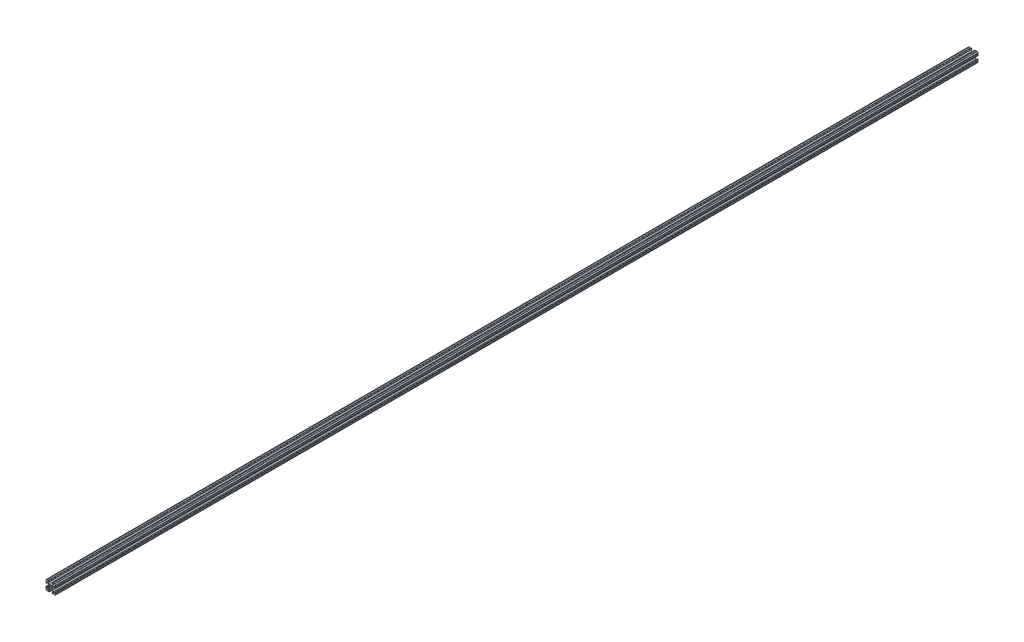
SolidWorks part; units mm, degrees
ref_plane "Front Plane" through (0, 0, 0) normal (0, 0, 1) x (1, 0, 0)
ref_plane "Top Plane" through (0, 0, 0) normal (0, 1, 0) x (1, 0, 0)
ref_plane "Right Plane" through (0, 0, 0) normal (1, 0, 0) x (0, 0, -1)
sketch "Sketch1" plane through (0, 0, 0) normal (0, 0, 1) x (1, 0, 0)
  line L0 (-12.7, -6.3331) -> (-12.7, -9.5504)
  line L1 (-9.5504, -12.7) -> (-6.3331, -12.7)
  line L2 (-5.3171, -12.7) -> (-4.3434, -12.7)
  line L3 (-4.3434, -10.4902) -> (-6.4748, -10.4902)
  line L4 (-7.1932, -8.7558) -> (-3.8632, -5.4257)
  line L5 (-1.6181, -4.4958) -> (1.6181, -4.4958)
  line L6 (3.8632, -5.4257) -> (7.1932, -8.7558)
  line L7 (6.4748, -10.4902) -> (4.3434, -10.4902)
  line L8 (4.3434, -12.7) -> (5.3171, -12.7)
  line L9 (6.3331, -12.7) -> (9.5504, -12.7)
  line L10 (12.7, -9.5504) -> (12.7, -6.3331)
  line L11 (12.7, -5.3171) -> (12.7, -4.3434)
  line L12 (10.4902, -4.3434) -> (10.4902, -6.4748)
  line L13 (8.7558, -7.1932) -> (5.4257, -3.8632)
  line L14 (4.4958, -1.6181) -> (4.4958, 1.6181)
  line L15 (5.4257, 3.8632) -> (8.7558, 7.1932)
  line L16 (10.4902, 6.4748) -> (10.4902, 4.3434)
  line L17 (12.7, 4.3434) -> (12.7, 5.3171)
  line L18 (12.7, 6.3331) -> (12.7, 9.5504)
  line L19 (9.5504, 12.7) -> (6.3331, 12.7)
  line L20 (5.3171, 12.7) -> (4.3434, 12.7)
  line L21 (4.3434, 10.4902) -> (6.4748, 10.4902)
  line L22 (7.1932, 8.7558) -> (3.8632, 5.4257)
  line L23 (1.6181, 4.4958) -> (-1.6181, 4.4958)
  line L24 (-3.8632, 5.4257) -> (-7.1932, 8.7558)
  line L25 (-6.4748, 10.4902) -> (-4.3434, 10.4902)
  line L26 (-4.3434, 12.7) -> (-5.3171, 12.7)
  line L27 (-6.3331, 12.7) -> (-9.5504, 12.7)
  line L28 (-12.7, 9.5504) -> (-12.7, 6.3331)
  line L29 (-12.7, 5.3171) -> (-12.7, 4.3434)
  line L30 (-10.4902, 4.3434) -> (-10.4902, 6.4748)
  line L31 (-8.7558, 7.1932) -> (-5.4257, 3.8632)
  line L32 (-4.4958, 1.6181) -> (-4.4958, -1.6181)
  line L33 (-5.4257, -3.8632) -> (-8.7558, -7.1932)
  line L34 (-10.4902, -6.4748) -> (-10.4902, -4.3434)
  line L35 (-12.7, -4.3434) -> (-12.7, -5.3171)
  circle A0 centre (0, 0) radius 2.6035
  arc A1 (-12.7, -5.3171) -> (-12.7, -6.3331) centre (-12.7, -5.8251) cw
  arc A2 (-12.7, -9.5504) -> (-12.6998, -10.5664) centre (-12.7, -10.0584) cw
  arc A3 (-12.6998, -10.5664) -> (-10.5664, -12.6998) centre (-10.5918, -10.5918) ccw
  arc A4 (-10.5664, -12.6998) -> (-9.5504, -12.7) centre (-10.0584, -12.7) cw
  arc A5 (-6.3331, -12.7) -> (-5.3171, -12.7) centre (-5.8251, -12.7) cw
  arc A6 (-4.3434, -12.7) -> (-4.3434, -10.4902) centre (-4.3434, -11.5951) ccw
  arc A7 (-6.4748, -10.4902) -> (-7.1932, -8.7558) centre (-6.4748, -9.4742) cw
  arc A8 (-3.8632, -5.4257) -> (-1.6181, -4.4958) centre (-1.6181, -7.6708) cw
  arc A9 (1.6181, -4.4958) -> (3.8632, -5.4257) centre (1.6181, -7.6708) cw
  arc A10 (7.1932, -8.7558) -> (6.4748, -10.4902) centre (6.4748, -9.4742) cw
  arc A11 (4.3434, -10.4902) -> (4.3434, -12.7) centre (4.3434, -11.5951) ccw
  arc A12 (5.3171, -12.7) -> (6.3331, -12.7) centre (5.8251, -12.7) cw
  arc A13 (9.5504, -12.7) -> (10.5664, -12.6998) centre (10.0584, -12.7) cw
  arc A14 (10.5664, -12.6998) -> (12.6998, -10.5664) centre (10.5918, -10.5918) ccw
  arc A15 (12.6998, -10.5664) -> (12.7, -9.5504) centre (12.7, -10.0584) cw
  arc A16 (12.7, -6.3331) -> (12.7, -5.3171) centre (12.7, -5.8251) cw
  arc A17 (12.7, -4.3434) -> (10.4902, -4.3434) centre (11.5951, -4.3434) ccw
  arc A18 (10.4902, -6.4748) -> (8.7558, -7.1932) centre (9.4742, -6.4748) cw
  arc A19 (5.4257, -3.8632) -> (4.4958, -1.6181) centre (7.6708, -1.6181) cw
  arc A20 (4.4958, 1.6181) -> (5.4257, 3.8632) centre (7.6708, 1.6181) cw
  arc A21 (8.7558, 7.1932) -> (10.4902, 6.4748) centre (9.4742, 6.4748) cw
  arc A22 (10.4902, 4.3434) -> (12.7, 4.3434) centre (11.5951, 4.3434) ccw
  arc A23 (12.7, 5.3171) -> (12.7, 6.3331) centre (12.7, 5.8251) cw
  arc A24 (12.7, 9.5504) -> (12.6998, 10.5664) centre (12.7, 10.0584) cw
  arc A25 (12.6998, 10.5664) -> (10.5664, 12.6998) centre (10.5918, 10.5918) ccw
  arc A26 (10.5664, 12.6998) -> (9.5504, 12.7) centre (10.0584, 12.7) cw
  arc A27 (6.3331, 12.7) -> (5.3171, 12.7) centre (5.8251, 12.7) cw
  arc A28 (4.3434, 12.7) -> (4.3434, 10.4902) centre (4.3434, 11.5951) ccw
  arc A29 (6.4748, 10.4902) -> (7.1932, 8.7558) centre (6.4748, 9.4742) cw
  arc A30 (3.8632, 5.4257) -> (1.6181, 4.4958) centre (1.6181, 7.6708) cw
  arc A31 (-1.6181, 4.4958) -> (-3.8632, 5.4257) centre (-1.6181, 7.6708) cw
  arc A32 (-7.1932, 8.7558) -> (-6.4748, 10.4902) centre (-6.4748, 9.4742) cw
  arc A33 (-4.3434, 10.4902) -> (-4.3434, 12.7) centre (-4.3434, 11.5951) ccw
  arc A34 (-5.3171, 12.7) -> (-6.3331, 12.7) centre (-5.8251, 12.7) cw
  arc A35 (-9.5504, 12.7) -> (-10.5664, 12.6998) centre (-10.0584, 12.7) cw
  arc A36 (-10.5664, 12.6998) -> (-12.6998, 10.5664) centre (-10.5918, 10.5918) ccw
  arc A37 (-12.6998, 10.5664) -> (-12.7, 9.5504) centre (-12.7, 10.0584) cw
  arc A38 (-12.7, 6.3331) -> (-12.7, 5.3171) centre (-12.7, 5.8251) cw
  arc A39 (-12.7, 4.3434) -> (-10.4902, 4.3434) centre (-11.5951, 4.3434) ccw
  arc A40 (-10.4902, 6.4748) -> (-8.7558, 7.1932) centre (-9.4742, 6.4748) cw
  arc A41 (-5.4257, 3.8632) -> (-4.4958, 1.6181) centre (-7.6708, 1.6181) cw
  arc A42 (-4.4958, -1.6181) -> (-5.4257, -3.8632) centre (-7.6708, -1.6181) cw
  arc A43 (-8.7558, -7.1932) -> (-10.4902, -6.4748) centre (-9.4742, -6.4748) cw
  arc A44 (-10.4902, -4.3434) -> (-12.7, -4.3434) centre (-11.5951, -4.3434) ccw
extrude "Boss-Extrude1" add sketch "Sketch1" against normal blind 2438.4
